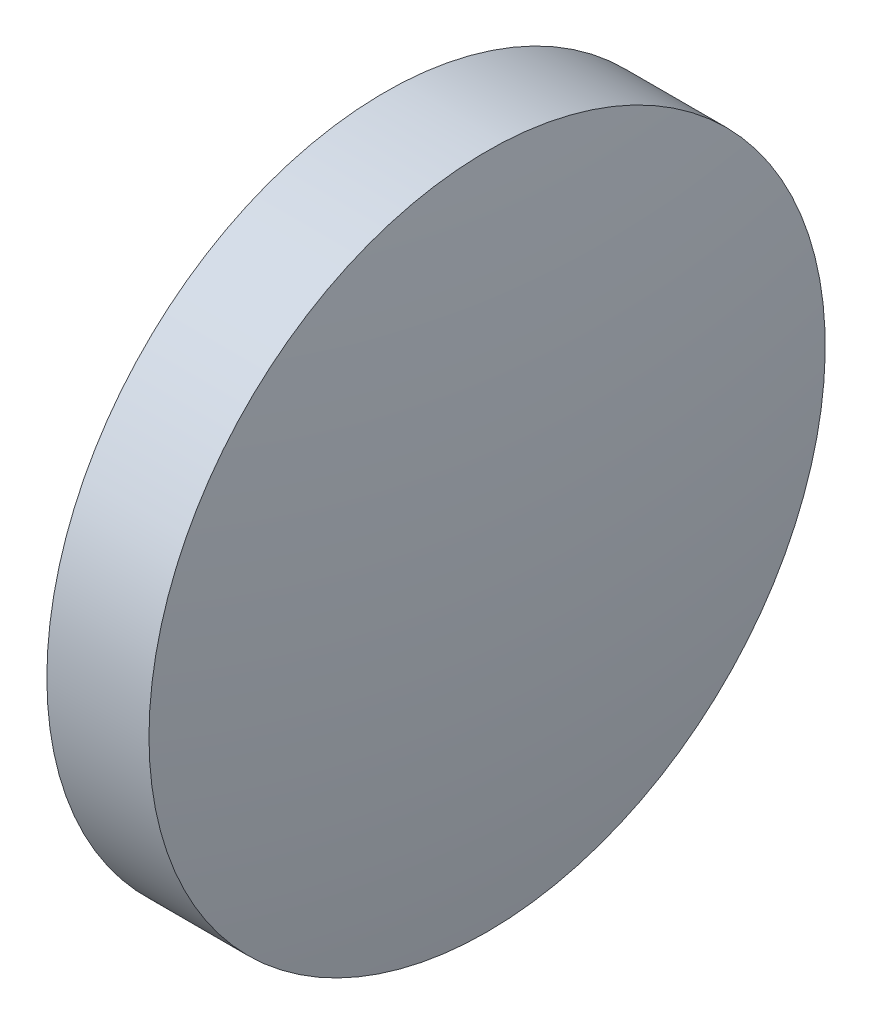
SolidWorks part; units mm, degrees
ref_plane "前视基准面" through (0, 0, 0) normal (0, 0, 1) x (1, 0, 0)
ref_plane "上视基准面" through (0, 0, 0) normal (0, 1, 0) x (1, 0, 0)
ref_plane "右视基准面" through (0, 0, 0) normal (1, 0, 0) x (0, 0, -1)
sketch "草图1" plane through (0, 0, 0) normal (0, 0, 1) x (1, 0, 0)
  line L0 (594.5262, 196.2413) -> (600.6616, 196.2413) construction
  line L1 (595.4678, 196.2413) -> (595.4678, 201.2413)
  line L2 (597.3678, 196.2413) -> (595.4678, 196.2413)
  line L5 (595.4678, 201.2413) -> (596.9778, 201.2413)
  arc A0 (597.3678, 196.2413) -> (596.9778, 201.2413) centre (565.1215, 196.2413) ccw
revolve "旋转1" add sketch "草图1" angle 360 about L0
